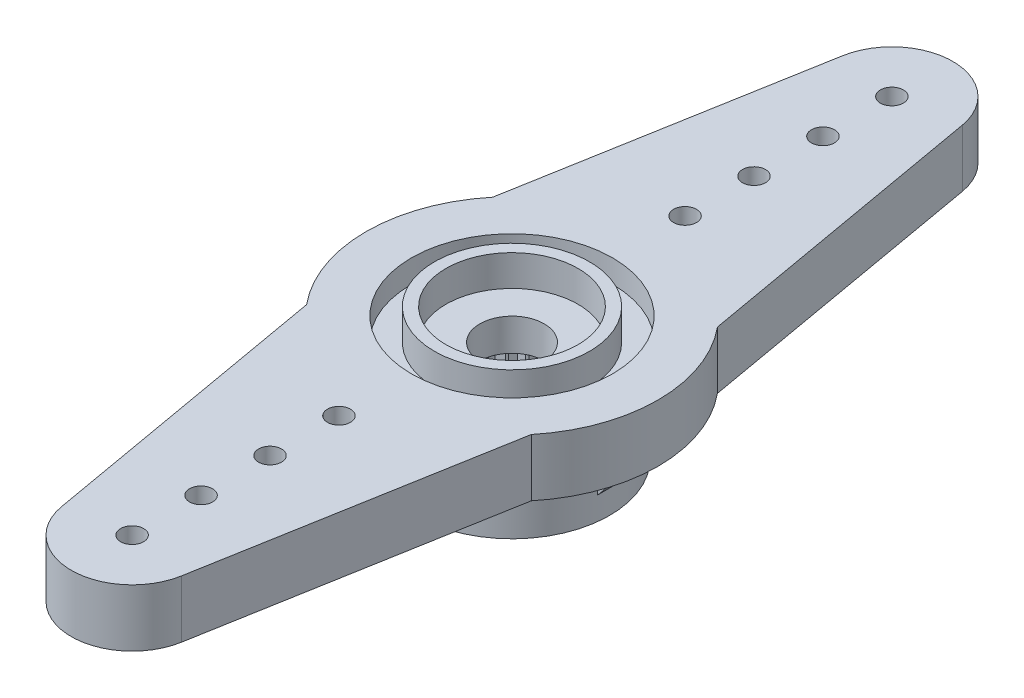
SolidWorks part; units mm, degrees
material "Polyethylene Cross-Linked"
ref_plane "Front Plane" through (0, 0, 0) normal (0, 0, 1) x (1, 0, 0)
ref_plane "Top Plane" through (0, 0, 0) normal (0, 1, 0) x (1, 0, 0)
ref_plane "Right Plane" through (0, 0, 0) normal (1, 0, 0) x (0, 0, -1)
sketch "Sketch1" plane through (0, 0, 0) normal (0, 1, 0) x (1, 0, 0)
  circle A0 centre (0, 0) radius 6.35
  dimension "D1" = 12.7
extrude "Boss-Extrude1" add sketch "Sketch1" along normal blind 5.4
sketch "Sketch2" plane through (0, 5.4, 0) normal (0, 1, 0) x (1, 0, 0)
  line L0 (0, 0) -> (0, 16.53) construction
  line L1 (-2.6097, 16.9902) -> (-4.8916, 4.049)
  line L2 (0, 19.18) -> (0, 16.53) construction
  line L3 (2.6097, 16.9902) -> (4.8916, 4.049)
  arc A0 (2.6097, 16.9902) -> (-2.6097, 16.9902) centre (0, 16.53) ccw
  arc A4 (4.8916, 4.049) -> (-4.8916, 4.049) centre (0, 0) ccw
  circle A5 centre (0, 0) radius 6.35 construction
  dimension "D1" = 5.3
  dimension "D2" = 19.18
  dimension "D3" = 10
  dimension "D4" = 9.7832
extrude "horn" add sketch "Sketch2" against normal blind 2.5
sketch "Sketch4" plane through (0, 5.4, 0) normal (0, -1, 0) x (-1, 0, 0)
  circle A0 centre (0, 0) radius 1.4
  dimension "D1" = 2.8
extrude "Cut-Extrude1" cut sketch "Sketch4" along normal through all
sketch "Sketch5" plane through (0, 0, 0) normal (0, -1, 0) x (-1, 0, 0)
  circle A0 centre (0, 16.53) radius 0.5
  dimension "D1" = 1
extrude "Cut-Extrude2" cut sketch "Sketch5" against normal through all
sketch "Sketch6" plane through (0, 0, 0) normal (0, 1, 0) x (1, 0, 0)
  line L0 (0, 0) -> (0, 16.53) construction
pattern_linear "LPattern1" count 4 spacing 3 along (0, 0, 1) of "Cut-Extrude2"
mirror "Mirror1" about plane through (0, 0, 0) normal (0, 0, 1) of "horn", "LPattern1", "Cut-Extrude2"
sketch "Sketch8" plane through (0, 0, 0) normal (0, -1, 0) x (-1, 0, 0)
  line L0 (0, -2.9) -> (0.2629, -2.5867)
  line L1 (0, -2.9) -> (-0.2629, -2.5867)
  line L2 (0, -2.6) -> (0, -2.9) construction
  line L3 (0, 0) -> (0, -2.6) construction
  arc A1 (-0.2629, -2.5867) -> (0.2629, -2.5867) centre (0, 0) ccw
  dimension "D1" = 0.3
  dimension "D2" = 5.2
  dimension "D3" = 80
extrude "Cut-Extrude4" cut sketch "Sketch8" against normal blind 3
pattern_circular "CirPattern2" count 26 over 360 about axis through (0, 0, 0) along (0, 1, 0) of "Cut-Extrude4"
sketch "Sketch9" plane through (0, 0, 0) normal (0, -1, 0) x (-1, 0, 0)
  circle A0 centre (0, 0) radius 2.6
  arc A1 (-0.2629, -2.5867) -> (0.2629, -2.5867) centre (0, 0) ccw construction
extrude "Cut-Extrude5" cut sketch "Sketch9" against normal blind 3
sketch "Sketch10" plane through (0, 0, 0) normal (0, -1, 0) x (-1, 0, 0)
  circle A0 centre (0, 0) radius 6.35
  circle A1 centre (0, 0) radius 4.25
  circle A2 centre (0, 0) radius 6.35 construction
  dimension "D1" = 8.5
extrude "Cut-Extrude6" cut sketch "Sketch10" against normal up to surface (2.9 mm away) up to face at (0, 2.9, 11.03)
sketch "Sketch11" plane through (0, 0, 0) normal (0, 0, 1) x (1, 0, 0)
  line L2 (4.21, 0.99) -> (5.8127, 2.9)
  line L3 (4.8916, 2.9) -> (6.35, 2.9) construction
  line L4 (5.8127, 2.9) -> (4.21, 2.9)
  line L7 (4.21, 0.99) -> (4.16, 0.99)
  line L8 (4.16, 0.99) -> (4.16, 2.9)
  line L10 (4.21, 0.99) -> (4.21, 2.9) construction
  line L12 (4.16, 2.9) -> (4.21, 2.9)
  line L13 (0, 2.9) -> (4.16, 2.9) construction
  line L14 (-4.25, 2.9) -> (4.25, 2.9) construction
  dimension "D1" = 1.91
  dimension "D2" = 0.05
  dimension "D3" = 40
  dimension "D4" = 4.16
extrude "Boss-Extrude5" add sketch "Sketch11" along normal mid plane 1
pattern_circular "CirPattern3" count 4 over 360 about axis through (0, 0, 0) along (0, 1, 0) of "Boss-Extrude5"
sketch "Sketch12" plane through (0, 5.4, 0) normal (0, 1, 0) x (1, 0, 0)
  circle A0 centre (0, 0) radius 4.375
  dimension "D1" = 8.75
extrude "Cut-Extrude7" cut sketch "Sketch12" against normal blind 1
sketch "Sketch13" plane through (0, 4.4, 0) normal (0, 1, 0) x (1, 0, 0)
  circle A0 centre (0, 0) radius 2.875
  circle A1 centre (0, 0) radius 3.375
  dimension "D1" = 0.5
  dimension "D2" = 6.75
extrude "Boss-Extrude6" add sketch "Sketch13" along normal up to surface (1 mm away)
sketch "Sketch14" plane through (0, 5.4, 0) normal (0, 1, 0) x (1, 0, 0)
  circle A0 centre (0, 0) radius 2.875
  circle A1 centre (0, 0) radius 2.875 construction
  circle A2 centre (0, 0) radius 3.375
  circle A3 centre (0, 0) radius 3.375 construction
extrude "Boss-Extrude7" add sketch "Sketch14" along normal blind 0.35
